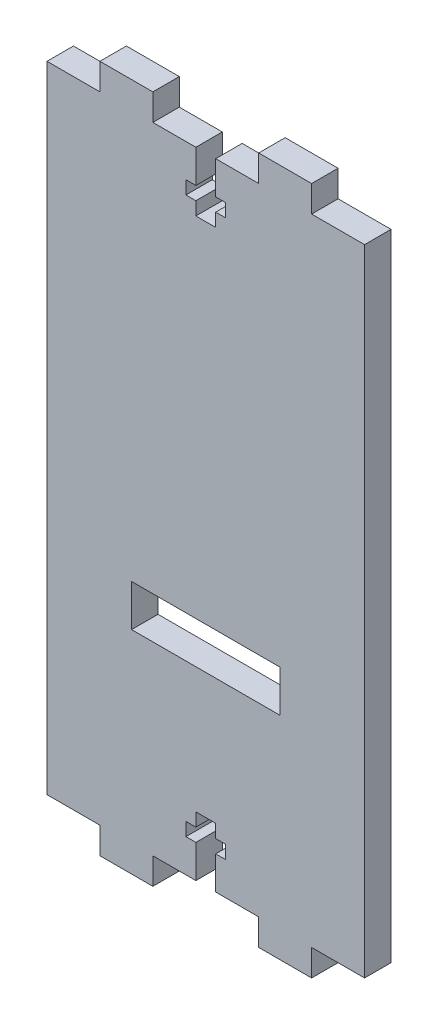
SolidWorks part; units mm, degrees
ref_plane "Front Plane" through (0, 0, 0) normal (0, 0, 1) x (1, 0, 0)
ref_plane "Top Plane" through (0, 0, 0) normal (0, 1, 0) x (1, 0, 0)
ref_plane "Right Plane" through (0, 0, 0) normal (1, 0, 0) x (0, 0, -1)
sketch "Sketch2" plane through (0, 0, 0) normal (0, 0, 1) x (1, 0, 0)
  line L1 (12.2447, 6.35) -> (12.2447, 0)
  line L2 (-0.4553, 6.35) -> (-0.4553, 158.75)
  line L3 (-0.4553, 158.75) -> (12.2447, 158.75)
  line L4 (75.7447, 6.35) -> (75.7447, 158.75)
  line L5 (-0.4553, 6.35) -> (12.2447, 6.35)
  line L6 (40.0259, 6.35) -> (50.3447, 6.35)
  line L7 (40.0259, 158.75) -> (40.0259, 150.8125)
  line L8 (12.2447, 0) -> (24.9447, 0)
  line L9 (24.9447, 6.35) -> (35.2634, 6.35)
  line L10 (24.9447, 0) -> (24.9447, 6.35)
  line L11 (40.0259, 150.8125) -> (42.4072, 150.8125)
  line L12 (50.3447, 6.35) -> (50.3447, 0)
  line L13 (63.0447, 6.35) -> (75.7447, 6.35)
  line L14 (63.0447, 6.35) -> (63.0447, 0)
  line L15 (40.0259, 147.6375) -> (42.4072, 147.6375)
  line L16 (42.4072, 150.8125) -> (42.4072, 147.6375)
  line L17 (40.0259, 17.4625) -> (40.0259, 20.6375)
  line L18 (35.2634, 147.6375) -> (35.2634, 144.4625)
  line L19 (50.3447, 0) -> (63.0447, 0)
  line L20 (40.0259, 144.4625) -> (35.2634, 144.4625)
  line L21 (35.2634, 6.35) -> (35.2634, 14.2875)
  line L22 (35.2634, 14.2875) -> (32.8822, 14.2875)
  line L23 (32.8822, 150.8125) -> (32.8822, 147.6375)
  line L24 (35.2634, 17.4625) -> (32.8822, 17.4625)
  line L25 (32.8822, 14.2875) -> (32.8822, 17.4625)
  line L26 (35.2634, 147.6375) -> (32.8822, 147.6375)
  line L27 (35.2634, 150.8125) -> (32.8822, 150.8125)
  line L28 (35.2634, 158.75) -> (35.2634, 150.8125)
  line L29 (50.3447, 165.1) -> (63.0447, 165.1)
  line L30 (40.0259, 147.6375) -> (40.0259, 144.4625)
  line L31 (63.0447, 158.75) -> (63.0447, 165.1)
  line L32 (40.0259, 20.6375) -> (35.2634, 20.6375)
  line L33 (35.2634, 17.4625) -> (35.2634, 20.6375)
  line L34 (63.0447, 158.75) -> (75.7447, 158.75)
  line L35 (42.4072, 14.2875) -> (42.4072, 17.4625)
  line L36 (40.0259, 17.4625) -> (42.4072, 17.4625)
  line L37 (50.3447, 158.75) -> (50.3447, 165.1)
  line L38 (40.0259, 14.2875) -> (42.4072, 14.2875)
  line L39 (40.0259, 6.35) -> (40.0259, 14.2875)
  line L40 (24.9447, 158.75) -> (24.9447, 165.1)
  line L41 (24.9447, 158.75) -> (35.2634, 158.75)
  line L42 (12.2447, 158.75) -> (12.2447, 165.1)
  line L43 (40.0259, 158.75) -> (50.3447, 158.75)
  line L44 (12.2447, 165.1) -> (24.9447, 165.1)
  line L45 (-0.4553, 158.75) -> (12.2447, 158.75)
  line L46 (40.0259, 158.75) -> (50.3447, 158.75)
  line L47 (24.9447, 158.75) -> (35.2634, 158.75)
  line L48 (63.0447, 158.75) -> (75.7447, 158.75)
  line L49 (22.6447, 60.8) -> (52.6447, 60.8)
  line L50 (22.6447, 60.8) -> (22.6447, 50.8)
  line L51 (22.6447, 50.8) -> (52.6447, 50.8)
  line L52 (52.6447, 60.8) -> (52.6447, 50.8)
  dimension "D2" = 30
  dimension "D3" = 10
  dimension "D4" = 50.8
  dimension "D5" = 6.35
  dimension "D6" = 12.7
  dimension "D7" = 12.7
  dimension "D8" = 12.7
  dimension "D9" = 23.1
  dimension "D10" = 10.3188
  dimension "D11" = 2.3813
  dimension "D12" = 7.9375
  dimension "D13" = 3.175
  dimension "D14" = 3.175
  dimension "D15" = 25.4
  dimension "D16" = 12.7
  dimension "D17" = 10.3187
  dimension "D18" = 4.7625
extrude "Boss-Extrude1" add sketch "Sketch2" along normal blind 6.35 contours L44 L42 L3 L2 L5 L1 L8 L10 L9 L21 L22 L25 L24 L33 L32 L17 L36 L35 L38 L39 L6 L12 L19 L14 L13 L4 L34 L31 L29 L37 L43 L7 L11 L16 L15 L30 L20 L18 L26 L23 L27 L28 L41 L40 L49 L52 L51 L50
sketch "Sketch3" plane through (0, 0, 6.35) normal (0, 0, 1) x (1, 0, 0)
  line L1 (19.8434, 50.8) -> (55.4034, 50.8)
  line L2 (19.8434, 50.8) -> (19.8434, 60.8)
  line L3 (19.8434, 60.8) -> (55.4034, 60.8)
  line L4 (55.4034, 50.8) -> (55.4034, 60.8)
  line L5 (19.8434, 50.8) -> (55.4034, 60.8) construction
  line L6 (19.8434, 60.8) -> (55.4034, 50.8) construction
  point P0 (37.6234, 55.8)
  dimension "D1" = 35.56
extrude "Cut-Extrude1" cut sketch "Sketch3" against normal blind 6.35
